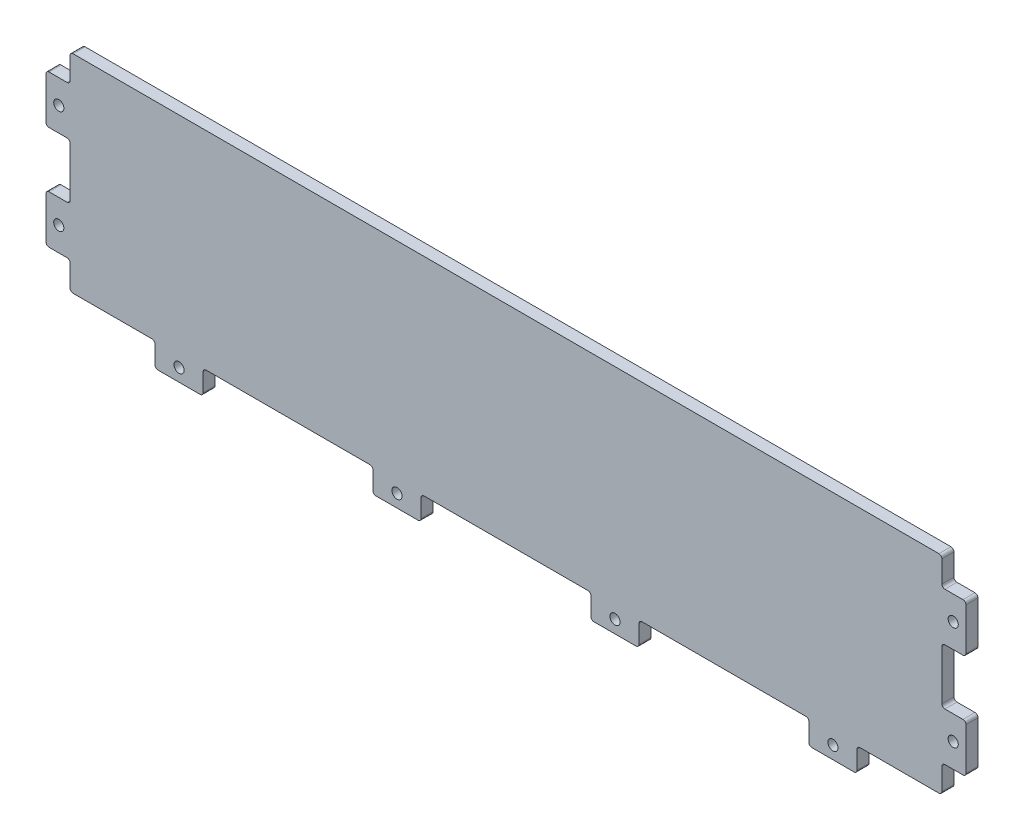
SolidWorks part; units mm, degrees
material "PE High Density"
ref_plane "Front Plane" through (0, 0, 0) normal (0, 0, 1) x (1, 0, 0)
ref_plane "Top Plane" through (0, 0, 0) normal (0, 1, 0) x (1, 0, 0)
ref_plane "Right Plane" through (0, 0, 0) normal (1, 0, 0) x (0, 0, -1)
sketch "Sketch1" plane through (0, 0, 0) normal (0, 0, 1) x (1, 0, 0)
  line L1 (-457.2, -109.5375) -> (457.2, -109.5375)
  line L2 (-460.375, -106.3625) -> (-460.375, 106.3625)
  line L3 (-457.2, 109.5375) -> (457.2, 109.5375)
  line L4 (460.375, -106.3625) -> (460.375, 106.3625)
  line L5 (-460.375, -109.5375) -> (460.375, 109.5375) construction
  line L6 (-460.375, 109.5375) -> (460.375, -109.5375) construction
  arc A0 (457.2, 109.5375) -> (460.375, 106.3625) centre (457.2, 106.3625) cw
  arc A1 (457.2, -109.5375) -> (460.375, -106.3625) centre (457.2, -106.3625) ccw
  arc A2 (-457.2, -109.5375) -> (-460.375, -106.3625) centre (-457.2, -106.3625) cw
  arc A3 (-460.375, 106.3625) -> (-457.2, 109.5375) centre (-457.2, 106.3625) cw
  point P0 (0, 0)
  dimension "D3" = 3.175
  dimension "D1" = 920.75
  dimension "D2" = 219.075
extrude "Boss-Extrude1" add sketch "Sketch1" along normal mid plane 12.7
sketch "Sketch2" plane through (0, 0, 0) normal (0, 0, 1) x (1, 0, 0)
  line L0 (-460.375, 106.3625) -> (-460.375, -106.3625) construction
  line L1 (-460.375, 80.1687) -> (-482.6, 80.1687)
  line L2 (-460.375, 80.1687) -> (-460.375, 29.3687)
  line L3 (-460.375, 29.3687) -> (-482.6, 29.3687)
  line L4 (-485.775, 76.9937) -> (-485.775, 32.5437)
  line L5 (-457.2, -109.5375) -> (457.2, -109.5375) construction
  line L6 (-460.375, -29.3688) -> (-482.6, -29.3688)
  line L8 (-460.375, -80.1688) -> (-482.6, -80.1688)
  line L9 (-485.775, -32.5438) -> (-485.775, -76.9938)
  line L11 (-370.6812, -109.5375) -> (-370.6812, -131.7625)
  line L12 (-367.5062, -134.9375) -> (-323.0562, -134.9375)
  line L13 (-319.8812, -109.5375) -> (-319.8812, -131.7625)
  line L14 (-460.375, -54.7688) -> (-460.375, -109.5375) construction
  line L15 (-460.375, 106.3625) -> (-460.375, -106.3625) construction
  line L17 (-140.4937, -109.5375) -> (-140.4937, -131.7625)
  line L18 (-137.3187, -134.9375) -> (-92.8687, -134.9375)
  line L19 (-89.6937, -109.5375) -> (-89.6937, -131.7625)
  line L25 (-460.375, -109.5375) -> (-345.2812, -109.5375) construction
  line L39 (-460.375, -54.7688) -> (-460.375, 0) construction
  line L40 (-460.375, -29.3688) -> (-460.375, -80.1688)
  line L41 (-370.6812, -109.5375) -> (-319.8812, -109.5375)
  line L42 (-140.4937, -109.5375) -> (-89.6937, -109.5375)
  line L43 (-345.2812, -109.5375) -> (-230.1875, -109.5375) construction
  line L55 (-460.375, 0) -> (-460.375, 54.7687) construction
  line L56 (-460.375, 54.7687) -> (-460.375, 109.5375) construction
  line L58 (-457.2, -109.5375) -> (457.2, -109.5375) construction
  line L59 (-230.1875, -109.5375) -> (-115.0937, -109.5375) construction
  line L60 (-115.0937, -109.5375) -> (0, -109.5375) construction
  arc A0 (-92.8687, -134.9375) -> (-89.6937, -131.7625) centre (-92.8687, -131.7625) ccw
  arc A1 (-140.4937, -131.7625) -> (-137.3187, -134.9375) centre (-137.3187, -131.7625) ccw
  arc A2 (-323.0562, -134.9375) -> (-319.8812, -131.7625) centre (-323.0562, -131.7625) ccw
  arc A3 (-370.6812, -131.7625) -> (-367.5062, -134.9375) centre (-367.5062, -131.7625) ccw
  arc A4 (-482.6, -80.1688) -> (-485.775, -76.9938) centre (-482.6, -76.9938) cw
  arc A5 (-482.6, -29.3688) -> (-485.775, -32.5438) centre (-482.6, -32.5438) ccw
  arc A6 (-482.6, 29.3687) -> (-485.775, 32.5437) centre (-482.6, 32.5437) cw
  arc A7 (-482.6, 80.1687) -> (-485.775, 76.9937) centre (-482.6, 76.9937) ccw
  point P60 (-485.775, 29.3687)
  point P63 (-485.775, 80.1687)
  dimension "D9" = 3.175
  dimension "D1" = 50.8
  dimension "D2" = 25.4
  dimension "D7" = 25.4
extrude "Tabs" add sketch "Sketch2" along normal mid plane 12.7
mirror "Mirror1" about plane through (0, 0, 0) normal (1, 0, 0) of "Tabs"
fillet "Fillet1" radius 3.175 16 edges at (-89.6937, -109.5375, 0) (-140.4937, -109.5375, 0) (-319.8812, -109.5375, 0) (-370.6812, -109.5375, 0) (-460.375, -80.1688, 0) (-460.375, -29.3688, 0) (-460.375, 29.3687, 0) (-460.375, 80.1687, 0) (460.375, 29.3687, 0) (460.375, 80.1687, 0) (460.375, -29.3688, 0) (460.375, -80.1688, 0) (319.8812, -109.5375, 0) (89.6937, -109.5375, 0) (370.6812, -109.5375, 0) (140.4937, -109.5375, 0)
sketch "Sketch3" plane through (0, 0, 0) normal (0, 0, 1) x (1, 0, 0)
  line L0 (-473.075, 80.1687) -> (-473.075, 29.3687) construction
  line L3 (-463.55, 80.1687) -> (-482.6, 80.1687) construction
  line L6 (-485.775, 76.9937) -> (-485.775, 32.5437) construction
  line L7 (-485.775, -32.5438) -> (-485.775, -76.9938) construction
  line L8 (-367.5062, -134.9375) -> (-323.0562, -134.9375) construction
  line L9 (-137.3187, -134.9375) -> (-92.8687, -134.9375) construction
  line L10 (-482.6, 29.3687) -> (-463.55, 29.3687) construction
  line L11 (-473.075, -29.3688) -> (-473.075, -80.1688) construction
  line L12 (-463.55, -29.3688) -> (-482.6, -29.3688) construction
  line L13 (-482.6, -80.1688) -> (-463.55, -80.1688) construction
  line L14 (-460.375, 26.1937) -> (-460.375, -26.1938) construction
  line L15 (-370.6812, -122.2375) -> (-319.8812, -122.2375) construction
  line L16 (-370.6812, -112.7125) -> (-370.6812, -131.7625) construction
  line L18 (-140.4937, -122.2375) -> (-89.6937, -122.2375) construction
  line L21 (-316.7062, -109.5375) -> (-143.6688, -109.5375) construction
  line L22 (-319.8812, -131.7625) -> (-319.8812, -112.7125) construction
  line L23 (-140.4937, -112.7125) -> (-140.4937, -131.7625) construction
  line L24 (-89.6937, -131.7625) -> (-89.6937, -112.7125) construction
  circle A0 centre (-472.2812, 54.7687) radius 5.3578
  circle A1 centre (-472.2812, -54.7688) radius 5.3578
  circle A2 centre (-345.2812, -121.4438) radius 5.3578
  circle A3 centre (-115.0937, -121.4438) radius 5.3578
  point P17 (-485.775, 54.7687)
  point P25 (-485.775, -54.7688)
  point P28 (-345.2812, -134.9375)
  point P31 (-115.0937, -134.9375)
  dimension "D1" = 10.7156
  dimension "D2" = 12.7
  dimension "D4" = 12.7
  dimension "D3" = 0.7937
  dimension "D5" = 0.7937
  dimension "D6" = 12.7
extrude "Cable Tie hole" cut sketch "Sketch3" against normal through all both and the other way through all
mirror "Mirror2" about plane through (0, 0, 0) normal (1, 0, 0) of "Cable Tie hole"
equation "\"D5@Sketch3\"=\"D3@Sketch3\""
equation "\"D7@Sketch2\"=\"D2@Sketch2\""
equation "\"D4@Sketch3\"=\"D6@Sketch3\""
